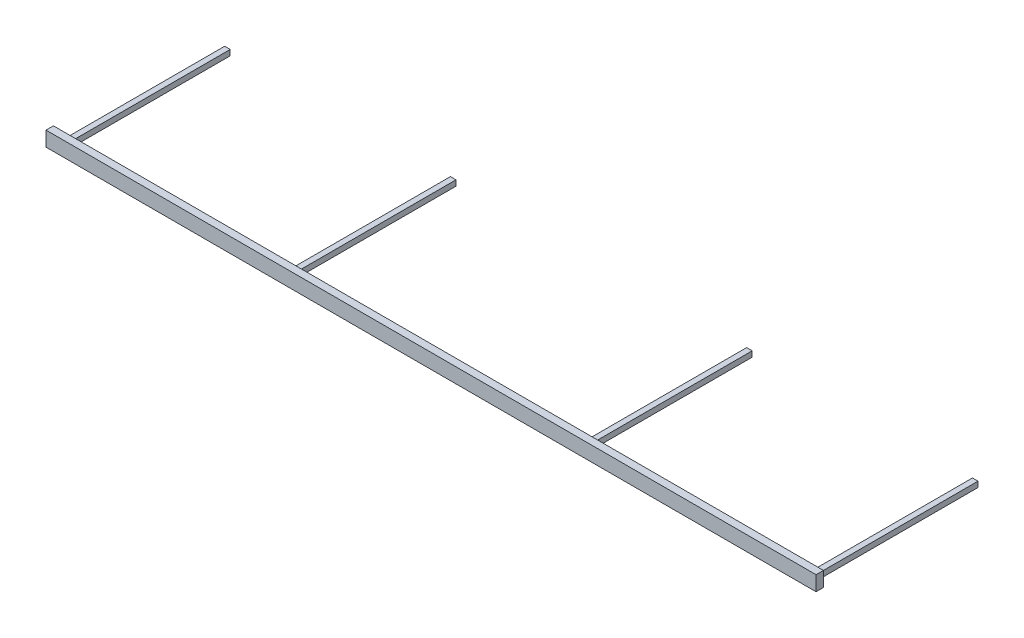
SolidWorks part; units mm, degrees
material "2014-T4"
ref_plane "Front Plane" through (0, 0, 0) normal (0, 0, 1) x (1, 0, 0)
ref_plane "Top Plane" through (0, 0, 0) normal (0, 1, 0) x (1, 0, 0)
ref_plane "Right Plane" through (0, 0, 0) normal (1, 0, 0) x (0, 0, -1)
sketch "Sketch1" plane through (0, 0, 0) normal (1, 0, 0) x (0, 0, -1)
  line L0 (-10.16, 22.86) -> (-10.16, -22.86)
  line L1 (-12.7, 25.4) -> (12.7, 25.4)
  line L2 (-12.7, 25.4) -> (-12.7, -25.4)
  line L3 (-12.7, -25.4) -> (12.7, -25.4)
  line L4 (12.7, 25.4) -> (12.7, -25.4)
  line L5 (-12.7, 25.4) -> (12.7, -25.4) construction
  line L6 (-12.7, -25.4) -> (12.7, 25.4) construction
  line L7 (-10.16, -22.86) -> (10.16, -22.86)
  line L8 (10.16, 22.86) -> (10.16, -22.86)
  line L9 (-10.16, 22.86) -> (10.16, 22.86)
  point P0 (0, 0)
  dimension "D1" = 25.4
  dimension "D2" = 50.8
  dimension "D3" = 2.54
extrude "Boss-Extrude1" add sketch "Sketch1" along normal mid plane 2628.9
sketch "Sketch2" plane through (1314.45, 0, 0) normal (1, 0, 0) x (0, 0, -1)
  line L0 (12.7, -25.4) -> (12.7, 25.4) construction
  line L1 (-12.7, 25.4) -> (12.7, 25.4)
  line L2 (-12.7, 25.4) -> (-12.7, -25.4)
  line L3 (-12.7, -25.4) -> (12.7, -25.4)
  line L4 (12.7, 25.4) -> (12.7, -25.4)
  line L5 (-12.7, 25.4) -> (12.7, -25.4) construction
  line L6 (-12.7, -25.4) -> (12.7, 25.4) construction
  line L7 (12.7, 25.4) -> (-12.7, 25.4) construction
  point P0 (0, 0)
extrude "Boss-Extrude2" add sketch "Sketch2" along normal blind 6.35
sketch "Sketch3" plane through (-1314.45, 0, 0) normal (-1, 0, 0) x (0, 0, 1)
  line L0 (12.7, 25.4) -> (12.7, -25.4) construction
  line L1 (-12.7, 25.4) -> (12.7, 25.4)
  line L2 (-12.7, 25.4) -> (-12.7, -25.4)
  line L3 (-12.7, -25.4) -> (12.7, -25.4)
  line L4 (12.7, 25.4) -> (12.7, -25.4)
  line L5 (-12.7, 25.4) -> (12.7, -25.4) construction
  line L6 (-12.7, -25.4) -> (12.7, 25.4) construction
  line L7 (-12.7, 25.4) -> (12.7, 25.4) construction
  point P0 (0, 0)
extrude "Boss-Extrude3" add sketch "Sketch3" along normal blind 6.35
sketch "Sketch4" plane through (0, 0, -12.7) normal (0, 0, -1) x (-1, 0, 0)
  line L0 (-1320.8, -25.4) -> (1320.8, -25.4) construction
  line L1 (-1292.098, -3.175) -> (-1273.048, -3.175)
  line L2 (-1292.098, -3.175) -> (-1292.098, -22.225)
  line L3 (-1292.098, -22.225) -> (-1273.048, -22.225)
  line L4 (-1273.048, -3.175) -> (-1273.048, -22.225)
  line L5 (-1292.098, -3.175) -> (-1273.048, -22.225) construction
  line L6 (-1292.098, -22.225) -> (-1273.048, -3.175) construction
  line L7 (-1320.8, -25.4) -> (-1320.8, 25.4) construction
  line L8 (-1288.923, -6.35) -> (-1288.923, -19.05)
  line L9 (-1288.923, -19.05) -> (-1276.223, -19.05)
  line L10 (-1276.223, -6.35) -> (-1276.223, -19.05)
  line L11 (-1288.923, -6.35) -> (-1276.223, -6.35)
  line L36 (-517.525, -3.175) -> (-498.475, -3.175)
  line L45 (-517.525, -3.175) -> (-517.525, -22.225)
  line L46 (-517.525, -22.225) -> (-498.475, -22.225)
  line L47 (-498.475, -3.175) -> (-498.475, -22.225)
  line L48 (-517.525, -3.175) -> (-498.475, -22.225) construction
  line L49 (-517.525, -22.225) -> (-498.475, -3.175) construction
  line L50 (-514.35, -6.35) -> (-514.35, -19.05)
  line L51 (-514.35, -19.05) -> (-501.65, -19.05)
  line L52 (-501.65, -6.35) -> (-501.65, -19.05)
  line L53 (-514.35, -6.35) -> (-501.65, -6.35)
  line L54 (1273.048, -3.175) -> (1292.098, -3.175)
  line L55 (1273.048, -3.175) -> (1273.048, -22.225)
  line L56 (1273.048, -22.225) -> (1292.098, -22.225)
  line L57 (1292.098, -3.175) -> (1292.098, -22.225)
  line L58 (1273.048, -3.175) -> (1292.098, -22.225) construction
  line L59 (1273.048, -22.225) -> (1292.098, -3.175) construction
  line L60 (1276.223, -6.35) -> (1276.223, -19.05)
  line L61 (1276.223, -19.05) -> (1288.923, -19.05)
  line L62 (1288.923, -6.35) -> (1288.923, -19.05)
  line L63 (1276.223, -6.35) -> (1288.923, -6.35)
  line L64 (1320.8, 25.4) -> (1320.8, -25.4) construction
  line L65 (498.475, -3.175) -> (517.525, -3.175)
  line L66 (498.475, -3.175) -> (498.475, -22.225)
  line L67 (498.475, -22.225) -> (517.525, -22.225)
  line L68 (517.525, -3.175) -> (517.525, -22.225)
  line L69 (498.475, -3.175) -> (517.525, -22.225) construction
  line L70 (498.475, -22.225) -> (517.525, -3.175) construction
  line L71 (501.65, -6.35) -> (501.65, -19.05)
  line L72 (501.65, -19.05) -> (514.35, -19.05)
  line L73 (514.35, -6.35) -> (514.35, -19.05)
  line L74 (501.65, -6.35) -> (514.35, -6.35)
  point P0 (-1282.573, -12.7)
  point P13 (-508, -12.7)
  point P22 (1282.573, -12.7)
  point P33 (508, -12.7)
  point P42 (-1320.8, 0)
  dimension "D1" = 19.05
  dimension "D2" = 19.05
  dimension "D3" = 3.175
  dimension "D4" = 47.752
  dimension "D7" = 19.05
  dimension "D8" = 3.175
  dimension "D6" = 19.05
  dimension "D9" = 3.175
  dimension "D10" = 812.8
  dimension "D11" = 19.05
  dimension "D12" = 19.05
  dimension "D13" = 47.752
  dimension "D14" = 3.175
  dimension "D15" = 3.175
  dimension "D16" = 19.05
  dimension "D17" = 19.05
  dimension "D18" = 3.175
  dimension "D19" = 3.175
  dimension "D20" = 812.8
  dimension "D5" = 3.175
extrude "Boss-Extrude4" add sketch "Sketch4" along normal blind 558.8
